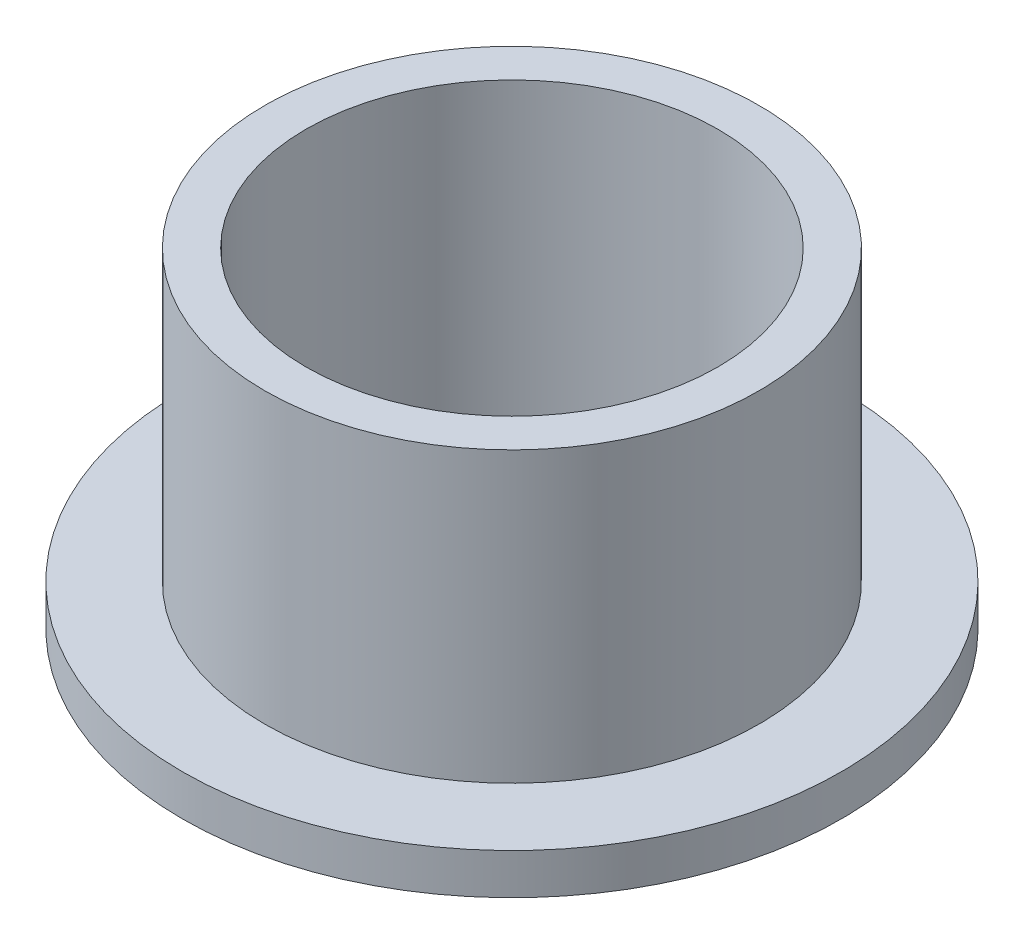
SolidWorks part; units mm, degrees
ref_plane "Front Plane" through (0, 0, 0) normal (0, 0, 1) x (1, 0, 0)
ref_plane "Top Plane" through (0, 0, 0) normal (0, 1, 0) x (1, 0, 0)
ref_plane "Right Plane" through (0, 0, 0) normal (1, 0, 0) x (0, 0, -1)
sketch "Sketch1" plane through (0, 0, 0) normal (0, 0, 1) x (1, 0, 0)
  line L0 (0, 26.7127) -> (0, 0) construction
  line L1 (7.9375, 0) -> (12.7, 0)
  line L2 (12.7, 0) -> (12.7, 1.5748)
  line L3 (12.7, 1.5748) -> (9.525, 1.5748)
  line L4 (9.525, 1.5748) -> (9.525, 12.7)
  line L5 (9.525, 12.7) -> (7.9375, 12.7)
  line L6 (7.9375, 12.7) -> (7.9375, 0)
  dimension "D1" = 15.875
  dimension "D2" = 19.05
  dimension "D3" = 25.4
  dimension "D4" = 12.7
  dimension "D5" = 1.5748
revolve "Revolve1" add sketch "Sketch1" angle 360 about L0
